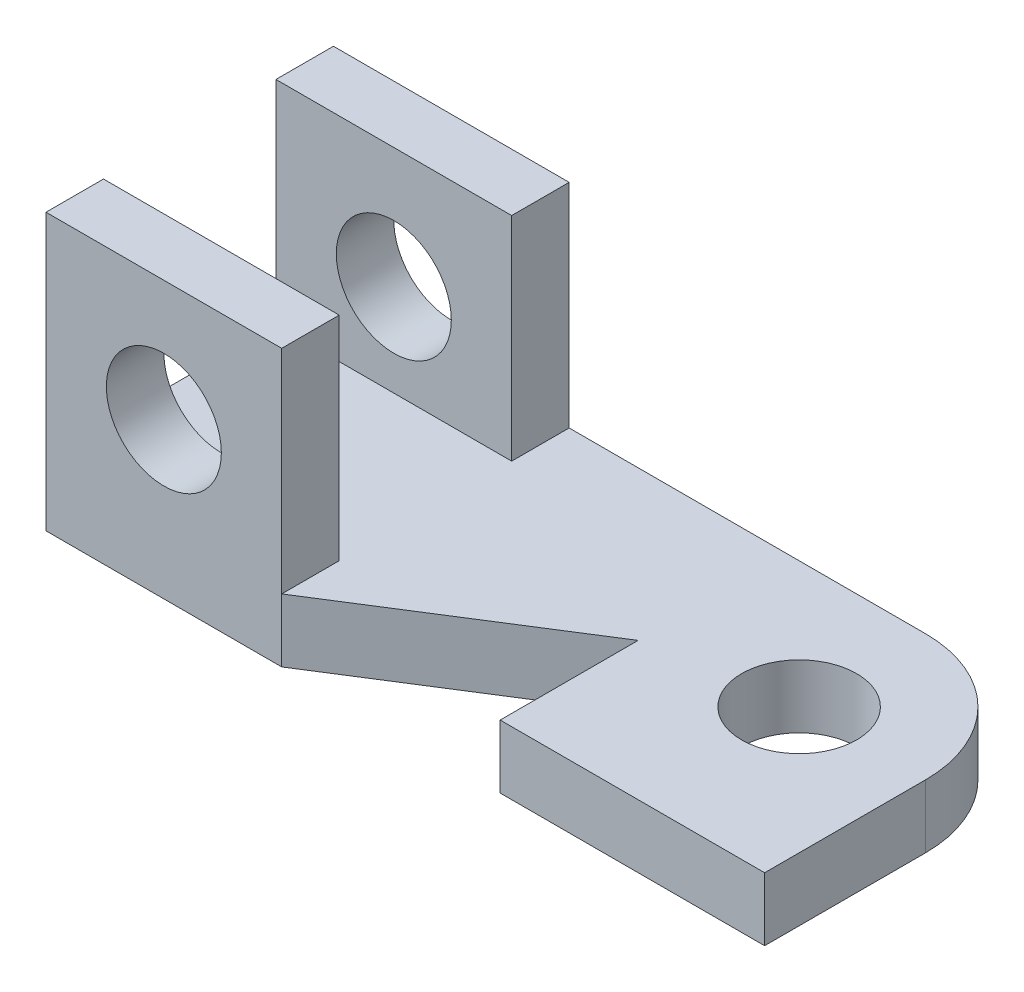
SolidWorks part; units mm, degrees
ref_plane "Front Plane" through (0, 0, 0) normal (0, 0, 1) x (1, 0, 0)
ref_plane "Top Plane" through (0, 0, 0) normal (0, 1, 0) x (1, 0, 0)
ref_plane "Right Plane" through (0, 0, 0) normal (1, 0, 0) x (0, 0, -1)
sketch "Sketch1" plane through (0, 0, 0) normal (0, 1, 0) x (1, 0, 0)
  line L0 (16.5, -25) -> (62.5, -25)
  line L1 (-62.5, -25) -> (-21.5, -25)
  line L2 (-62.5, -25) -> (-62.5, 25)
  line L3 (-62.5, 25) -> (62.5, 25)
  line L4 (62.5, -25) -> (62.5, 25)
  line L5 (-62.5, -25) -> (62.5, 25) construction
  line L6 (-62.5, 25) -> (62.5, -25) construction
  line L8 (-21.5, -25) -> (-21.5, 25) construction
  line L9 (16.5, -25) -> (16.5, -1)
  line L10 (16.5, -1) -> (-21.5, -25)
  point P0 (0, 0)
  dimension "D1" = 125
  dimension "D2" = 50
  dimension "D3" = 24
  dimension "D4" = 38
  dimension "D5" = 46
extrude "Boss-Extrude1" add sketch "Sketch1" along normal blind 11
sketch "Sketch2" plane through (0, 11, 0) normal (0, 1, 0) x (1, 0, 0)
  line L3 (62.5, -25) -> (62.5, 25) construction
  line L7 (62.5, 25) -> (-62.5, 25) construction
  circle A0 centre (40.5, 3) radius 10
  point P12 (37.276, 12.291)
  dimension "D2" = 20
  dimension "D1" = 22
  dimension "D3" = 22
extrude "Cut-Extrude1" cut sketch "Sketch2" against normal through all
sketch "Sketch3" plane through (0, 11, 0) normal (0, 1, 0) x (1, 0, 0)
  line L1 (-62.5, 25) -> (-21.5, 25)
  line L2 (-62.5, 25) -> (-62.5, 15)
  line L3 (-62.5, 15) -> (-21.5, 15)
  line L4 (-21.5, 25) -> (-21.5, 15)
  line L5 (-62.5, -25) -> (-21.5, -25)
  line L6 (-62.5, -25) -> (-62.5, -15)
  line L7 (-62.5, -15) -> (-21.5, -15)
  line L8 (-21.5, -25) -> (-21.5, -15)
  dimension "D1" = 41
  dimension "D2" = 41
  dimension "D3" = 10
  dimension "D4" = 10
extrude "Boss-Extrude2" add sketch "Sketch3" along normal blind 37
sketch "Sketch4" plane through (0, 0, 25) normal (0, 0, 1) x (1, 0, 0)
  line L1 (-62.5, 48) -> (-62.5, 0) construction
  line L2 (-62.5, 48) -> (-21.5, 48) construction
  circle A0 centre (-42, 27) radius 10
  dimension "D1" = 20
  dimension "D2" = 20.5
  dimension "D3" = 21
extrude "Cut-Extrude2" cut sketch "Sketch4" against normal through all
fillet "Fillet4" radius 22 1 edges at (62.5, 5.5, -25)
